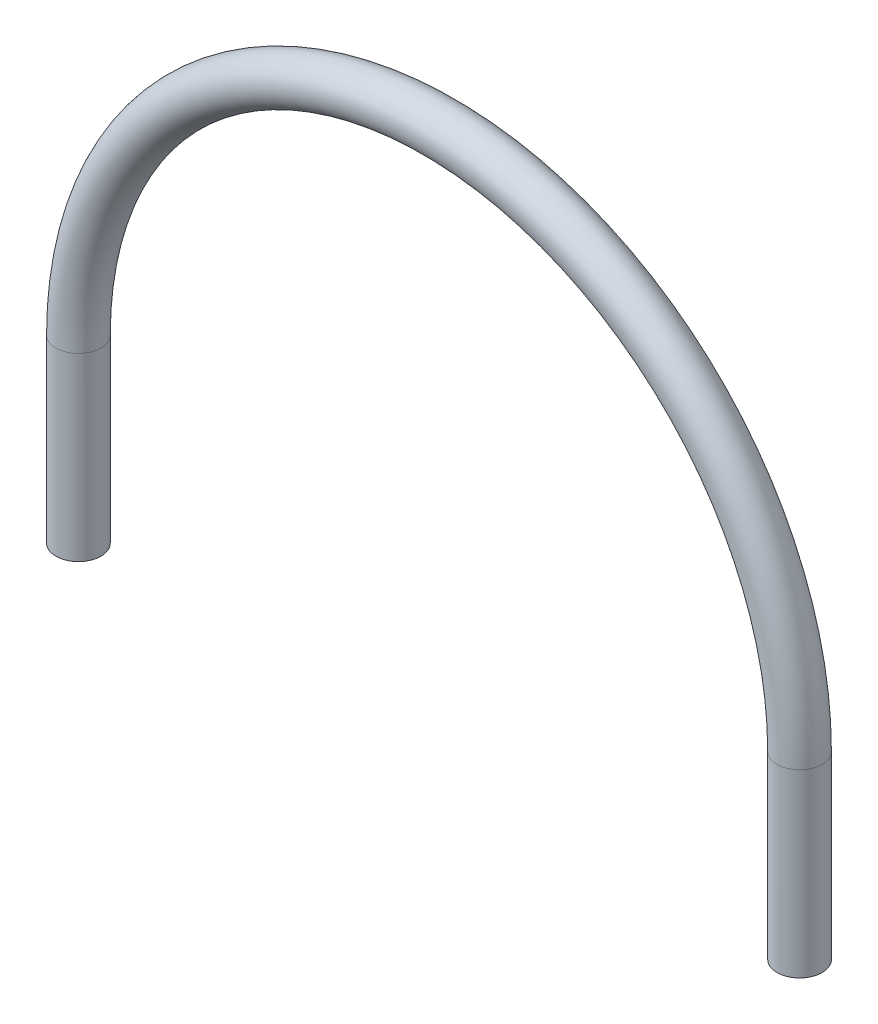
SolidWorks part; units mm, degrees
ref_plane "Front Plane" through (0, 0, 0) normal (0, 0, 1) x (1, 0, 0)
ref_plane "Top Plane" through (0, 0, 0) normal (0, 1, 0) x (1, 0, 0)
ref_plane "Right Plane" through (0, 0, 0) normal (1, 0, 0) x (0, 0, -1)
sketch "Sketch2" plane through (0, 0, 0) normal (0, 1, 0) x (1, 0, 0)
  circle A0 centre (-50.8, 0) radius 3.175
  dimension "D1" = 6.35
  dimension "D2" = 50.8
sketch "Sketch4" plane through (0, 0, 0) normal (0, 0, 1) x (1, 0, 0)
  line L0 (-47.625, 0) -> (-53.975, 0) construction
  arc A0 (-50.8, 0) -> (50.8, 0) centre (0, 0) cw
  point P6 (0, 0)
sweep "Sweep2" add profiles "Sketch2" path "Sketch4"
sketch "Sketch5" plane through (0, 0, 0) normal (0, -1, 0) x (1, 0, 0)
  circle A0 centre (-50.8, 0) radius 3.175
  circle A1 centre (50.8, 0) radius 3.175
  circle A2 centre (-50.8, 0) radius 3.175 construction
  circle A3 centre (50.8, 0) radius 3.175 construction
extrude "Boss-Extrude1" add sketch "Sketch5" along normal blind 25.4
